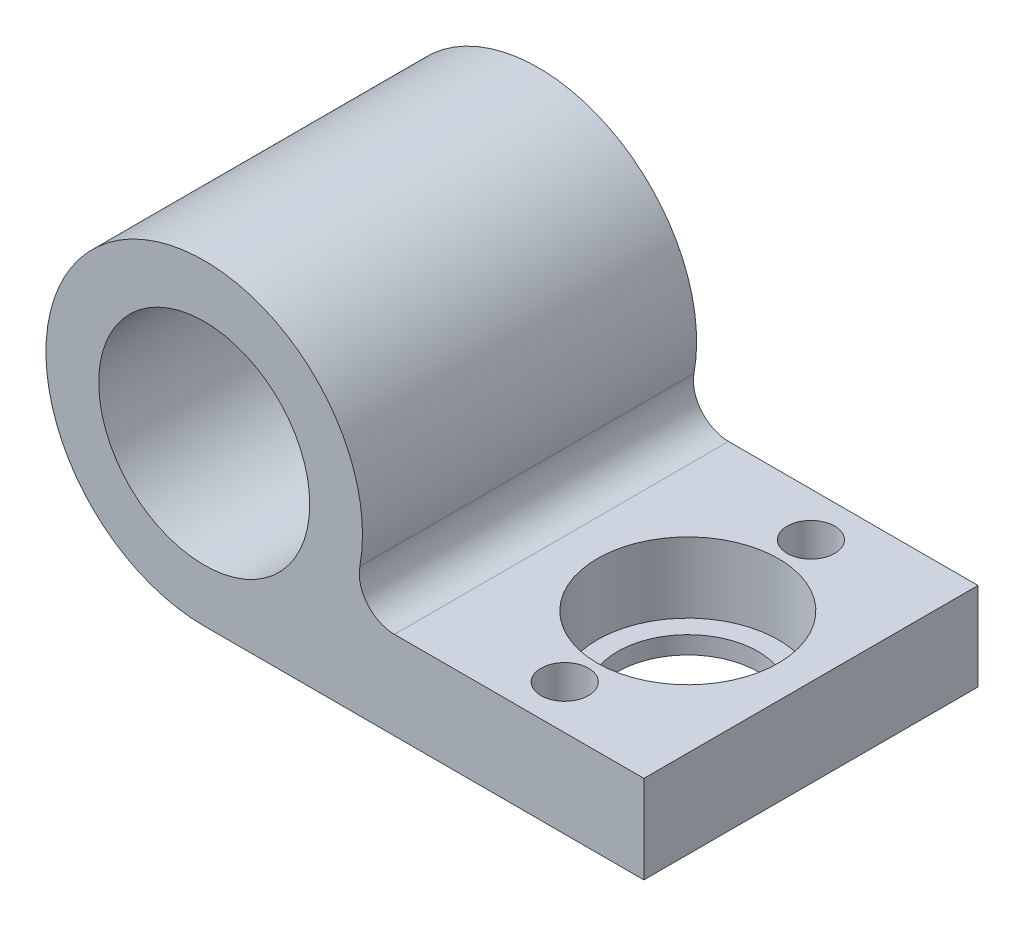
SolidWorks part; units mm, degrees
ref_plane "Front Plane" through (0, 0, 0) normal (0, 0, 1) x (1, 0, 0)
ref_plane "Top Plane" through (0, 0, 0) normal (0, 1, 0) x (1, 0, 0)
ref_plane "Right Plane" through (0, 0, 0) normal (1, 0, 0) x (0, 0, -1)
sketch "Sketch1" plane through (0, 0, 0) normal (0, 0, 1) x (1, 0, 0)
  circle A0 centre (0, 0) radius 6
  circle A1 centre (0, 0) radius 9
  dimension "D1" = 18
  dimension "D2" = 12
extrude "Main" add sketch "Sketch1" along normal mid plane 19
ref_plane "Plane1" through (0, -9, 0) normal (0, 1, 0) x (1, 0, 0)
sketch "Sketch2" plane through (0, -9, 0) normal (0, 1, 0) x (1, 0, 0)
  line L0 (9, 9.5) -> (-9, 9.5) construction
  line L1 (0, 9.5) -> (25, 9.5)
  line L2 (0, 9.5) -> (0, -9.5)
  line L3 (0, -9.5) -> (25, -9.5)
  line L4 (25, 9.5) -> (25, -9.5)
  line L5 (-9, -9.5) -> (9, -9.5) construction
  line L7 (18, 7) -> (18, -7) construction
  circle A0 centre (18, 0) radius 4
  circle A1 centre (18, 7) radius 1.35
  circle A2 centre (18, -7) radius 1.35
  point P15 (11.0946, -6.1874)
  point P16 (0, 0)
  dimension "D4" = 8
  dimension "D5" = 2.7
  dimension "D2" = 25
  dimension "D3" = 7
  dimension "D6" = 14
extrude "BallSupportExtrusion" add sketch "Sketch2" along normal blind 5
sketch "Sketch3" plane through (0, -4, 0) normal (0, 1, 0) x (1, 0, 0)
  circle A0 centre (18, 0) radius 5.15
  dimension "D1" = 10.3
extrude "BallSupportHole" cut sketch "Sketch3" against normal blind 4
fillet "Fillet2" radius 2 1 edges at (8.0623, -4, 0)
sketch "Sketch5" plane through (0, 0, 9.5) normal (0, 0, 1) x (1, 0, 0)
  circle A0 centre (0, 0) radius 6
  dimension "D1" = 12
extrude "Cut-Extrude2" cut sketch "Sketch5" against normal through all
